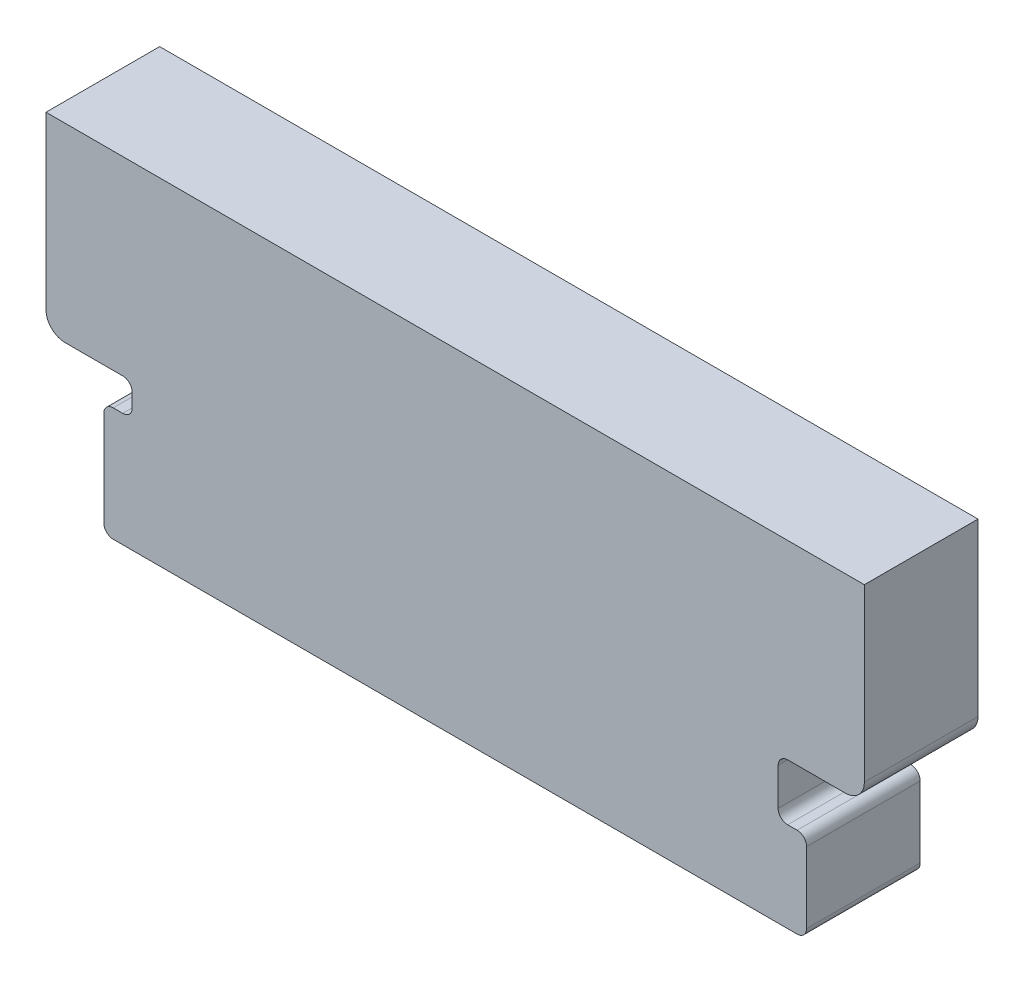
SolidWorks part; units mm, degrees
ref_plane "Front Plane" through (0, 0, 0) normal (0, 0, 1) x (1, 0, 0)
ref_plane "Top Plane" through (0, 0, 0) normal (0, 1, 0) x (1, 0, 0)
ref_plane "Right Plane" through (0, 0, 0) normal (1, 0, 0) x (0, 0, -1)
sketch "Sketch6" plane through (0, 0, 0) normal (0, 0, 1) x (1, 0, 0)
  line L0 (-18.05, -1.2595) -> (18.05, -1.2595)
  line L1 (18.55, -0.7595) -> (18.55, 2.9905)
  line L8 (18.05, 3.4905) -> (17.55, 3.4905)
  line L9 (17.05, 3.9905) -> (17.05, 5.9604)
  line L10 (17.55, 6.4604) -> (20.6, 6.4604)
  line L11 (21.6, 7.4604) -> (21.6, 16.4905)
  line L12 (21.6, 16.4905) -> (-21.6, 16.4905)
  line L14 (-21.6, 7.4604) -> (-21.6, 16.4905)
  line L15 (-17.55, 6.4604) -> (-20.6, 6.4604)
  line L16 (-17.05, 5.25) -> (-17.05, 5.9604)
  line L17 (-18.05, 4.75) -> (-17.55, 4.75)
  line L18 (-18.55, -0.7595) -> (-18.55, 4.25)
  arc A0 (-21.6, 7.4604) -> (-20.6, 6.4604) centre (-20.6, 7.4604) ccw
  arc A1 (-18.05, 4.75) -> (-18.55, 4.25) centre (-18.05, 4.25) ccw
  arc A2 (-17.05, 5.25) -> (-17.55, 4.75) centre (-17.55, 5.25) cw
  arc A3 (-17.55, 6.4604) -> (-17.05, 5.9604) centre (-17.55, 5.9604) cw
  arc A4 (17.05, 5.9604) -> (17.55, 6.4604) centre (17.55, 5.9604) cw
  arc A5 (17.55, 3.4905) -> (17.05, 3.9905) centre (17.55, 3.9905) cw
  arc A6 (18.55, 2.9905) -> (18.05, 3.4905) centre (18.05, 2.9905) ccw
  arc A7 (18.05, -1.2595) -> (18.55, -0.7595) centre (18.05, -0.7595) ccw
  arc A8 (-18.55, -0.7595) -> (-18.05, -1.2595) centre (-18.05, -0.7595) ccw
  arc A9 (20.6, 6.4604) -> (21.6, 7.4604) centre (20.6, 7.4604) ccw
  point P24 (17.05, 3.4905)
  point P27 (18.55, 3.4905)
  point P30 (18.55, -1.2595)
  dimension "D1" = 1
  dimension "D3" = 0.5
  dimension "D5" = 0.5
  dimension "D4" = 1.5
  dimension "D6" = 17.75
extrude "Boss-Extrude1" add sketch "Sketch6" along normal blind 6
